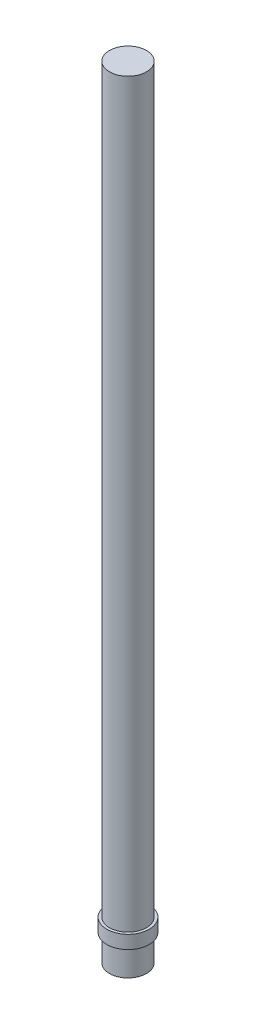
SolidWorks part; units mm, degrees
ref_plane "Front Plane" through (0, 0, 0) normal (0, 0, 1) x (1, 0, 0)
ref_plane "Top Plane" through (0, 0, 0) normal (0, 1, 0) x (1, 0, 0)
ref_plane "Right Plane" through (0, 0, 0) normal (1, 0, 0) x (0, 0, -1)
sketch "Sketch1" plane through (0, 0, 0) normal (0, 1, 0) x (1, 0, 0)
  circle A0 centre (0, 0) radius 3.5
  dimension "D1" = 7
extrude "Boss-Extrude1" add sketch "Sketch1" along normal blind 5
sketch "Sketch2" plane through (0, 5, 0) normal (0, 1, 0) x (1, 0, 0)
  circle A0 centre (0, 0) radius 4
  dimension "D1" = 8
extrude "Boss-Extrude2" add sketch "Sketch2" along normal blind 2.5
sketch "Sketch3" plane through (0, 7.5, 0) normal (0, 1, 0) x (1, 0, 0)
  circle A0 centre (0, 0) radius 3.5
  dimension "D1" = 7
extrude "Boss-Extrude3" add sketch "Sketch3" along normal blind 140
sketch "Sketch4" plane through (0, 147.5, 0) normal (0, 1, 0) x (1, 0, 0)
  circle A0 centre (0, 0) radius 3.25
  dimension "D1" = 6.5
